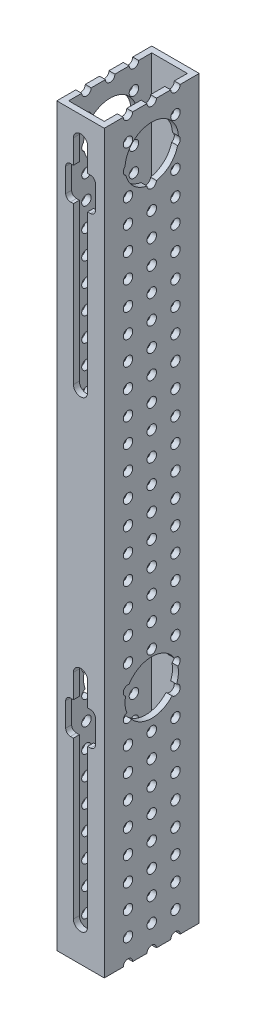
SolidWorks part; units mm, degrees
ref_plane "Front Plane" through (0, 0, 0) normal (0, 0, 1) x (1, 0, 0)
ref_plane "Top Plane" through (0, 0, 0) normal (0, 1, 0) x (1, 0, 0)
ref_plane "Right Plane" through (0, 0, 0) normal (1, 0, 0) x (0, 0, -1)
sketch "Sketch1" plane through (0, 0, 0) normal (0, 1, 0) x (1, 0, 0)
  line L1 (0, 0) -> (25.4, 0)
  line L2 (0, 0) -> (0, 50.8)
  line L3 (0, 50.8) -> (25.4, 50.8)
  line L4 (25.4, 0) -> (25.4, 50.8)
  dimension "D1" = 25.4
  dimension "D2" = 50.8
extrude "Boss-Extrude1" add sketch "Sketch1" along normal blind 419.1
shell "Shell1" thickness 3.175
sketch "Sketch2" plane through (0, 0, 0) normal (0, 0, 1) x (1, 0, 0)
  line L0 (12.7, 406.4) -> (12.7, 292.1) construction
  line L1 (16.51, 406.4) -> (16.51, 292.1)
  line L2 (8.89, 406.4) -> (8.89, 292.1)
  line L3 (0, 419.1) -> (25.4, 419.1) construction
  arc A0 (16.51, 406.4) -> (8.89, 406.4) centre (12.7, 406.4) ccw
  arc A1 (8.89, 292.1) -> (16.51, 292.1) centre (12.7, 292.1) ccw
  point P2 (12.7, 349.25)
  point P9 (12.7, 419.1)
  dimension "D1" = 7.62
  dimension "D2" = 114.3
  dimension "D3" = 12.7
extrude "Cut-Extrude1" cut sketch "Sketch2" against normal up to next (3.175 mm away)
sketch "Sketch3" plane through (25.4, 0, 0) normal (1, 0, 0) x (0, 0, -1)
  line L0 (3.175, 406.4) -> (0, 406.4) construction
  line L1 (3.175, 406.4) -> (0, 406.4) construction
  line L3 (0, 419.1) -> (50.8, 419.1) construction
  circle A0 centre (25.4, 394.97) radius 14.2875
  point P8 (25.4, 419.1)
  dimension "D1" = 28.575
  dimension "D2" = 11.43
extrude "Cut-Extrude2" cut sketch "Sketch3" against normal through all
sketch "Sketch4" plane through (0, 0, 0) normal (0, 0, 1) x (1, 0, 0)
  line L0 (16.51, 393.7) -> (18.0975, 393.7)
  line L1 (16.51, 406.4) -> (16.51, 292.1) construction
  line L2 (20.6375, 391.16) -> (20.6375, 378.46)
  line L3 (18.0975, 375.92) -> (16.51, 375.92)
  line L4 (12.7, 406.4) -> (12.7, 292.1) construction
  line L5 (12.7, 406.4) -> (12.7, 292.1) construction
  line L6 (7.3025, 375.92) -> (8.89, 375.92)
  line L7 (4.7625, 391.16) -> (4.7625, 378.46)
  line L8 (8.89, 393.7) -> (7.3025, 393.7)
  line L9 (8.89, 393.7) -> (16.51, 393.7)
  line L10 (8.89, 375.92) -> (16.51, 375.92)
  arc A0 (18.0975, 393.7) -> (20.6375, 391.16) centre (18.0975, 391.16) cw
  arc A1 (20.6375, 378.46) -> (18.0975, 375.92) centre (18.0975, 378.46) cw
  arc A2 (4.7625, 378.46) -> (7.3025, 375.92) centre (7.3025, 378.46) ccw
  arc A3 (7.3025, 393.7) -> (4.7625, 391.16) centre (7.3025, 391.16) ccw
  dimension "D1" = 2.54
  dimension "D5" = 2.54
  dimension "D2" = 1.5875
  dimension "D3" = 12.7
  dimension "D4" = 15.24
extrude "Cut-Extrude3" cut sketch "Sketch4" against normal up to next (3.175 mm away) contours A3 L7 A2 L6 L10 L3 A1 L2 A0 L0 L9 L8
pattern_linear "LPattern1" count 2 spacing 247.65 along (0, -1, 0) of "Cut-Extrude1", "Cut-Extrude2", "Cut-Extrude3"
sketch "Sketch6" plane through (0, 0, 0) normal (-1, 0, 0) x (0, 0, 1)
  line L0 (-50.8, 419.1) -> (-50.8, 0) construction
  line L1 (-50.8, 0) -> (0, 0) construction
  circle A0 centre (-38.1, 12.7) radius 2.54
  dimension "D1" = 5.08
  dimension "D2" = 12.7
  dimension "D3" = 12.7
extrude "Cut-Extrude4" cut sketch "Sketch6" against normal through all
pattern_linear "LPattern2" count 33 spacing 12.7 along (0, 1, 0) count 3 spacing 12.7 along (0, 0, 1) of "Cut-Extrude4"
sketch "Sketch7" plane through (0, 0, 0) normal (0, 0, 1) x (1, 0, 0)
  line L0 (0, 25.4) -> (25.4, 25.4)
  line L1 (0, 419.1) -> (0, 0) construction
  line L2 (0, 25.4) -> (12.573, 25.4) construction
  line L3 (25.4, 419.1) -> (25.4, 0) construction
  line L4 (12.827, 25.4) -> (25.4, 25.4) construction
  line L5 (0, 25.4) -> (0, 0)
  line L6 (0, 0) -> (25.4, 0)
  line L7 (25.4, 0) -> (25.4, 25.4)
extrude "Cut-Extrude5" cut sketch "Sketch7" against normal up to surface (50.8 mm away) up to face at (12.7, 209.55, -50.8)
